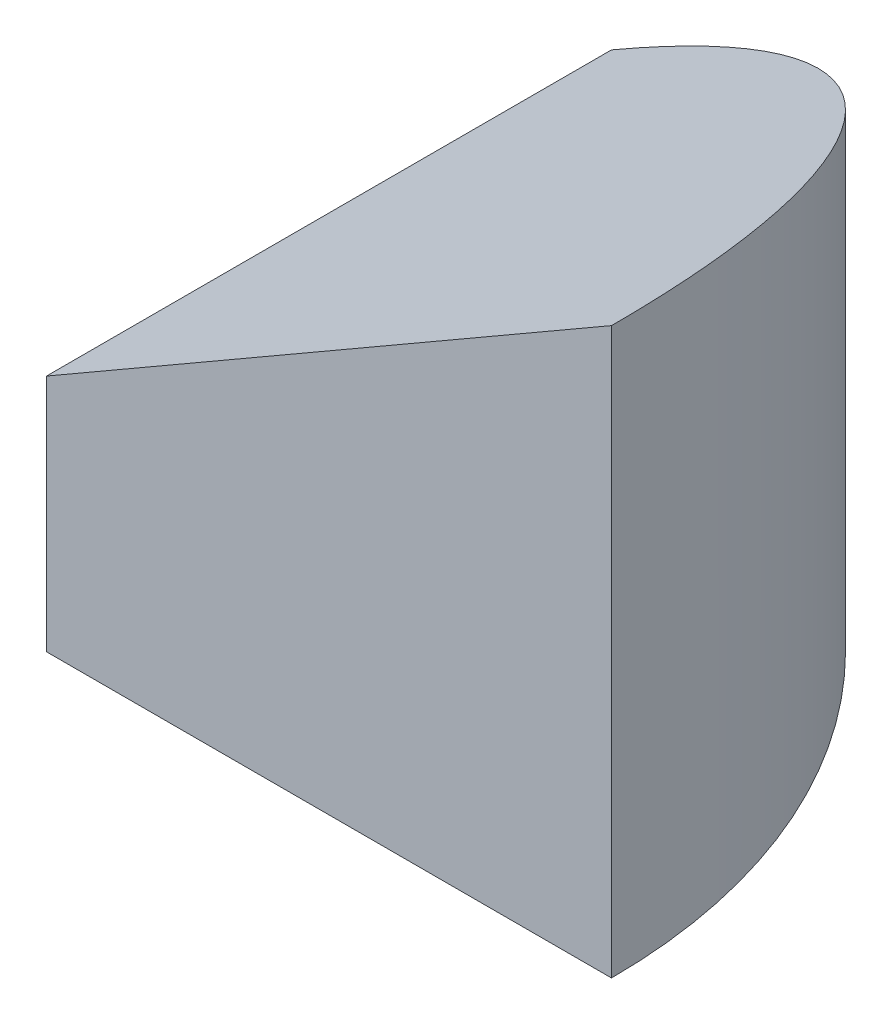
SolidWorks part; units mm, degrees
ref_plane "Plano frontal" through (0, 0, 0) normal (0, 0, 1) x (1, 0, 0)
ref_plane "Plano superior" through (0, 0, 0) normal (0, 1, 0) x (1, 0, 0)
ref_plane "Plano direito" through (0, 0, 0) normal (1, 0, 0) x (0, 0, -1)
sketch "Esboço1" plane through (0, 0, 0) normal (0, 1, 0) x (1, 0, 0)
  circle A0 centre (0, 0) radius 30
  dimension "D1" = 60
extrude "Ressalto-extrusão1" add sketch "Esboço1" along normal blind 30
sketch "Esboço2" plane through (0, 30, 0) normal (0, 1, 0) x (1, 0, 0)
  line L0 (0, 30) -> (0, 0)
  line L1 (0, 0) -> (30, 0)
  circle A0 centre (0, 0) radius 30 construction
  arc A1 (0, 30) -> (30, 0) centre (0, 0) ccw
extrude "Corte-extrusão1" cut sketch "Esboço2" against normal blind 30
sketch "Esboço3" plane through (0, 0, 0) normal (0, 0, 1) x (1, 0, 0)
  line L0 (30, 30) -> (0, 12.6795)
  line L2 (0, 12.6795) -> (0, 30)
  line L3 (0, 30) -> (30, 30)
  line L4 (30, 0) -> (0, 0) construction
  point P5 (0, 15)
  dimension "D1" = 30
extrude "Corte-extrusão2" cut sketch "Esboço3" against normal through all
